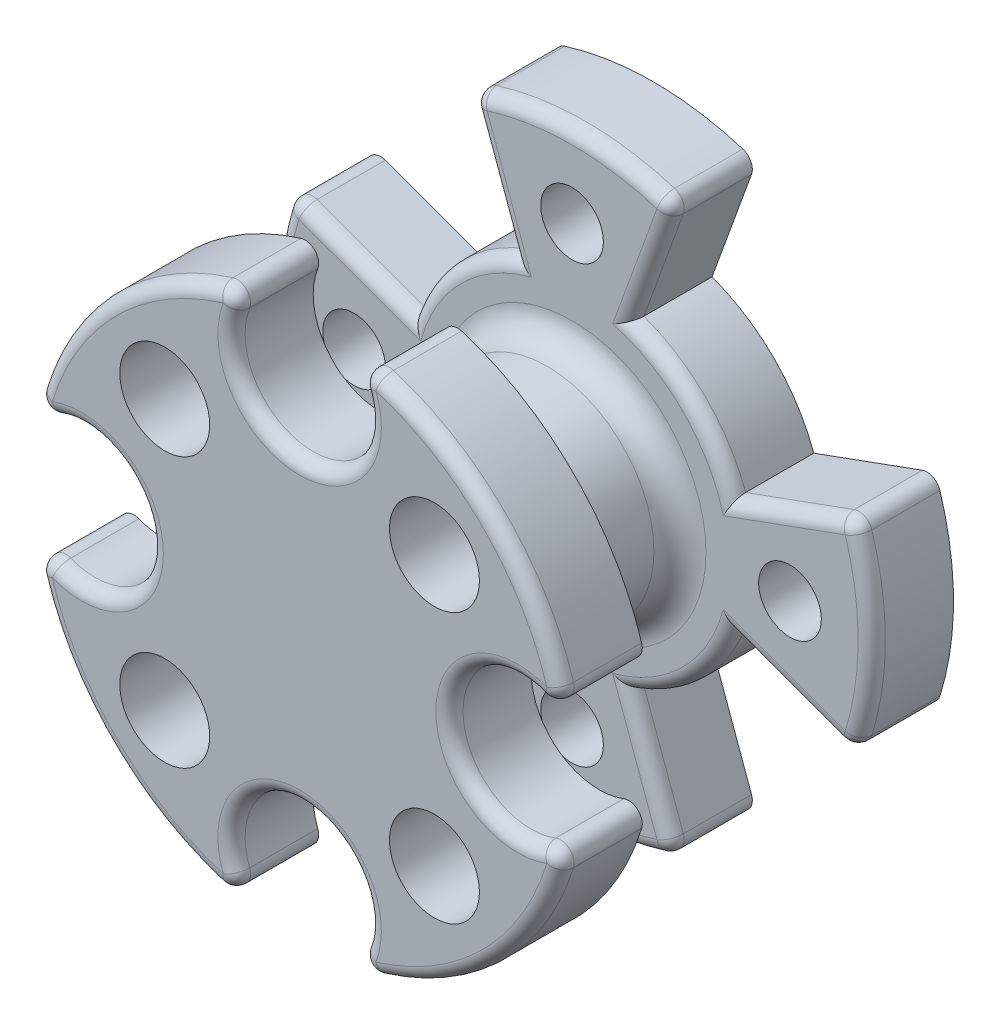
SolidWorks part; units mm, degrees
ref_plane "Front Plane" through (0, 0, 0) normal (0, 0, 1) x (1, 0, 0)
ref_plane "Top Plane" through (0, 0, 0) normal (0, 1, 0) x (1, 0, 0)
ref_plane "Right Plane" through (0, 0, 0) normal (1, 0, 0) x (0, 0, -1)
sketch "Sketch1" plane through (0, 0, 0) normal (0, 0, 1) x (1, 0, 0)
  circle A0 centre (0, 0) radius 11
  dimension "D1" = 22
extrude "Boss-Extrude1" add sketch "Sketch1" along normal blind 3
sketch "Sketch2" plane through (0, 0, 0) normal (0, 0, -1) x (-1, 0, 0)
  circle A0 centre (0, 0) radius 4.5
  dimension "D1" = 9
extrude "Cut-Extrude1" cut sketch "Sketch2" against normal blind 1.5
sketch "Sketch3" plane through (0, 0, 3) normal (0, 0, 1) x (1, 0, 0)
  circle A0 centre (0, 0) radius 8 construction
  circle A1 centre (0, 8) radius 1.15
  circle A2 centre (8, 0) radius 1.15
  circle A3 centre (0, -8) radius 1.15
  circle A4 centre (-8, 0) radius 1.15
  dimension "D1" = 16
  dimension "D2" = 2.3
extrude "Cut-Extrude2" cut sketch "Sketch3" against normal up to next
sketch "Sketch8" plane through (0, 0, 3) normal (0, 0, 1) x (1, 0, 0)
  line L0 (0, 0) -> (11, 0) construction
  line L1 (0, 0) -> (3.7622, 10.3366)
  line L2 (0, 0) -> (10.3366, 3.7622)
  line L3 (0, 0) -> (3.7622, -10.3366)
  line L4 (0, 0) -> (10.3366, -3.7622)
  line L5 (0, 0) -> (-10.3366, -3.7622)
  line L6 (0, 0) -> (-3.7622, -10.3366)
  line L7 (0, 0) -> (-3.7622, 10.3366)
  line L8 (0, 0) -> (-10.3366, 3.7622)
  circle A0 centre (0, 0) radius 6.25
  circle A1 centre (0, 0) radius 11 construction
  circle A2 centre (0, 0) radius 11
  circle M10 centre (0, 0) radius 11
  dimension "D1" = 12.5
  dimension "D2" = 20
  dimension "D3" = 70
  dimension "D4" = 4
extrude "Cut-Extrude4" cut sketch "Sketch8" against normal blind 10 contours A0 L2 L1 M10 | A0 L3 L4 M10 | A0 L5 L6 M10 | A0 L7 L8 M10
sketch "Sketch4" plane through (0, 0, 3) normal (0, 0, 1) x (1, 0, 0)
  circle A0 centre (0, 0) radius 4
  dimension "D1" = 8
extrude "Boss-Extrude2" add sketch "Sketch4" along normal blind 7 draft 5
sketch "Sketch6" plane through (0, 0, 10) normal (0, 0, 1) x (1, 0, 0)
  circle A0 centre (0, 0) radius 10
  dimension "D1" = 20
extrude "Boss-Extrude3" add sketch "Sketch6" along normal blind 3
sketch "Sketch7" plane through (0, 0, 13) normal (0, 0, 1) x (1, 0, 0)
  line L0 (0, 0) -> (-4.9497, 4.9497) construction
  line L1 (0, 0) -> (-7, 0) construction
  circle A0 centre (0, 0) radius 7 construction
  circle A5 centre (-4.9497, 4.9497) radius 1.65
  circle A6 centre (4.9497, 4.9497) radius 1.65
  circle A7 centre (4.9497, -4.9497) radius 1.65
  circle A8 centre (-4.9497, -4.9497) radius 1.65
  dimension "D1" = 14
  dimension "D2" = 45
  dimension "D3" = 3.3
  dimension "D4" = 4
extrude "Cut-Extrude3" cut sketch "Sketch7" against normal up to next
sketch "Sketch9" plane through (0, 0, 13) normal (0, 0, 1) x (1, 0, 0)
  circle A0 centre (8, 0) radius 2.5
  circle A1 centre (0, 8) radius 2.5
  circle A2 centre (-8, 0) radius 2.5
  circle A3 centre (0, -8) radius 2.5
  dimension "D1" = 5
extrude "Cut-Extrude5" cut sketch "Sketch9" against normal up to next
fillet "Fillet1" radius 1 1 edges at (4, 0, 3)
fillet "Fillet2" radius 0.5 40 edges at (5.5, 0, 13) (7.0711, 7.0711, 13) (0, 5.5, 13) (-7.0711, 7.0711, 13) (-5.5, 0, 13) (-7.0711, -7.0711, 13) (0, -5.5, 13) (-1.6711, -9.8594, 11.5) (1.6711, -9.8594, 11.5) (9.8594, -1.6711, 11.5) (9.8594, 1.6711, 11.5) (1.6711, 9.8594, 11.5) (-1.6711, 9.8594, 11.5) (-9.8594, 1.6711, 11.5) (-9.8594, -1.6711, 11.5) (-2.9499, -8.1048, 3) (-4.4194, -4.4194, 3) (0, -11, 3) (2.9499, -8.1048, 3) (4.4194, -4.4194, 3) (8.1048, -2.9499, 3) (8.1048, 2.9499, 3) (4.4194, 4.4194, 3) (2.9499, 8.1048, 3) (0, 11, 3) (-2.9499, 8.1048, 3) (-4.4194, 4.4194, 3) (-8.1048, 2.9499, 3) (-11, 0, 3) (-8.1048, -2.9499, 3) (-10.3366, 3.7622, 1.5) (-10.3366, -3.7622, 1.5) (-3.7622, -10.3366, 1.5) (3.7622, -10.3366, 1.5) (10.3366, -3.7622, 1.5) (10.3366, 3.7622, 1.5) (3.7622, 10.3366, 1.5) (-3.7622, 10.3366, 1.5) (7.0711, -7.0711, 13) (11, 0, 3)
